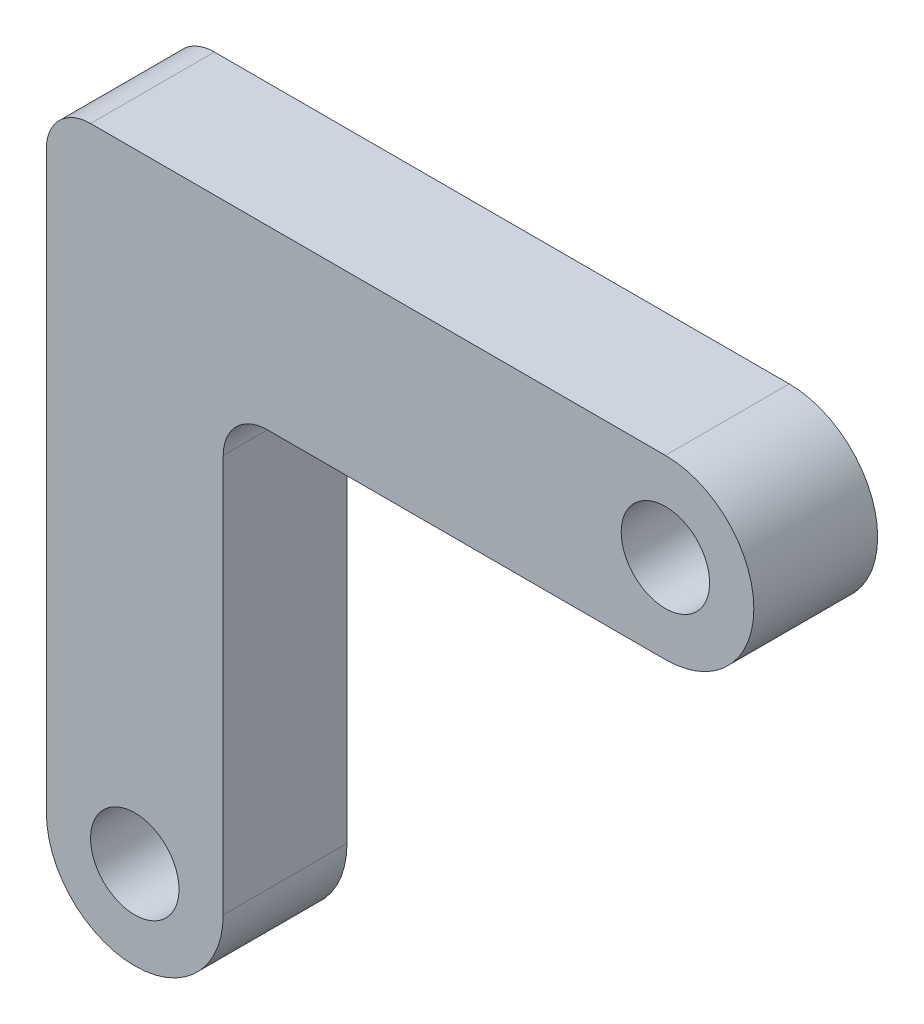
SolidWorks part; units mm, degrees
ref_plane "Front Plane" through (0, 0, 0) normal (0, 0, 1) x (1, 0, 0)
ref_plane "Top Plane" through (0, 0, 0) normal (0, 1, 0) x (1, 0, 0)
ref_plane "Right Plane" through (0, 0, 0) normal (1, 0, 0) x (0, 0, -1)
sketch "Sketch1" plane through (0, 0, 0) normal (0, 0, 1) x (1, 0, 0)
  line L0 (-0.9102, 0.713) -> (-0.9102, 14.713)
  line L4 (3.0898, 10.713) -> (3.0898, 0.713)
  line L7 (-0.9102, 14.713) -> (3.0898, 10.713) construction
  line L8 (3.0898, 10.713) -> (13.0898, 10.713)
  line L9 (13.0898, 14.713) -> (-0.9102, 14.713)
  circle A0 centre (1.0898, 0.713) radius 1
  arc A1 (-0.9102, 0.713) -> (3.0898, 0.713) centre (1.0898, 0.713) ccw
  arc A2 (13.0898, 14.713) -> (13.0898, 10.713) centre (13.0898, 12.713) cw
  circle A4 centre (13.0898, 12.713) radius 1
  dimension "D6" = 2
  dimension "D7" = 2
  dimension "D1" = 10
extrude "Boss-Extrude2" add sketch "Sketch1" along normal blind 2.8
fillet "Fillet1" radius 1 2 edges at (3.0898, 10.713, 1.4) (-0.9102, 14.713, 1.4)
